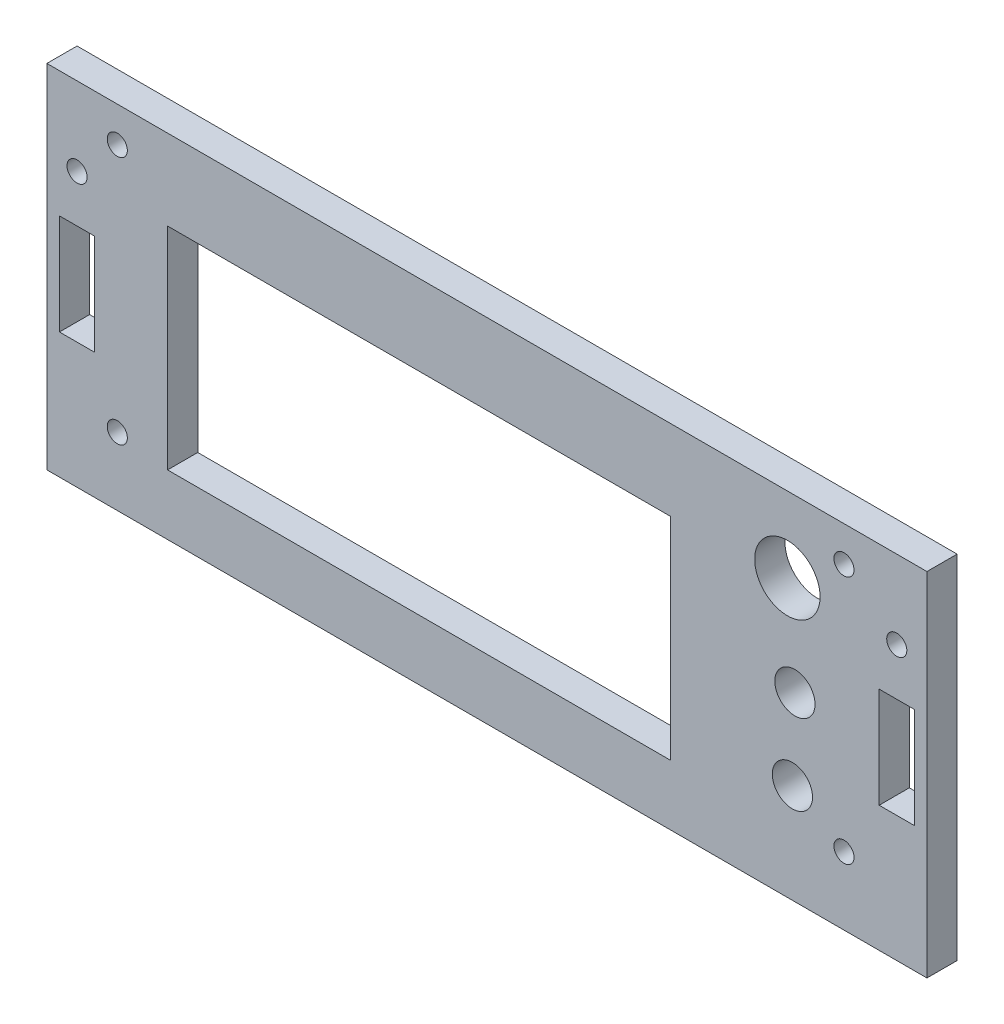
SolidWorks part; units mm, degrees
ref_plane "Plan de face" through (0, 0, 0) normal (0, 0, 1) x (1, 0, 0)
ref_plane "Plan de dessus" through (0, 0, 0) normal (0, 1, 0) x (1, 0, 0)
ref_plane "Plan de droite" through (0, 0, 0) normal (1, 0, 0) x (0, 0, -1)
sketch "Esquisse1" plane through (0, 0, 0) normal (0, 0, 1) x (1, 0, 0)
  line L1 (-87.5, 35) -> (87.5, 35)
  line L2 (-87.5, 35) -> (-87.5, -35)
  line L3 (-87.5, -35) -> (87.5, -35)
  line L4 (87.5, 35) -> (87.5, -35)
  line L5 (-87.5, 35) -> (87.5, -35) construction
  line L6 (-87.5, -35) -> (87.5, 35) construction
  line L7 (-63.5, 19) -> (36.5, 19)
  line L8 (-63.5, 19) -> (-63.5, -23)
  line L9 (-63.5, -23) -> (36.5, -23)
  line L10 (36.5, 19) -> (36.5, -23)
  line L11 (-63.5, 19) -> (36.5, -23) construction
  line L12 (-63.5, -23) -> (36.5, 19) construction
  point P0 (0, 0)
  point P6 (-13.5, -2)
  dimension "D1" = 175
  dimension "D2" = 70
  dimension "D3" = 100
  dimension "D4" = 42
  dimension "D5" = 24
  dimension "D6" = 12
extrude "Boss.-Extru.1" add sketch "Esquisse1" along normal blind 6
sketch "Esquisse2" plane through (0, 0, 6) normal (0, 0, 1) x (1, 0, 0)
  line L0 (-87.5, 0) -> (-81.5, 0) construction
  line L1 (-85, 10) -> (-78, 10)
  line L2 (-85, 10) -> (-85, -10)
  line L3 (-85, -10) -> (-78, -10)
  line L4 (-78, 10) -> (-78, -10)
  line L5 (-85, 10) -> (-78, -10) construction
  line L6 (-85, -10) -> (-78, 10) construction
  line L7 (-87.5, 35) -> (-87.5, -35) construction
  line L8 (-81.5, 0) -> (-81.5, 35) construction
  line L9 (87.5, 35) -> (-87.5, 35) construction
  circle A0 centre (-81.5, 19.4) radius 2
  point P0 (-81.5, 0)
  dimension "D4" = 4
  dimension "D1" = 7
  dimension "D2" = 20
  dimension "D3" = 6
  dimension "D5" = 15.6
extrude "Enlèv. mat.-Extru.1" cut sketch "Esquisse2" against normal blind 6
mirror "Symétrie1" about plane through (0, 0, 0) normal (1, 0, 0) of "Enlèv. mat.-Extru.1"
sketch "Esquisse3" plane through (0, 0, 6) normal (0, 0, 1) x (1, 0, 0)
  line L0 (-87.5, 35) -> (-87.5, -35) construction
  line L1 (-73.5, 28) -> (71, 28) construction
  line L2 (-73.5, 28) -> (-73.5, -21.5) construction
  line L3 (-73.5, -21.5) -> (71, -21.5) construction
  line L4 (71, 28) -> (71, -21.5) construction
  line L5 (-73.5, 28) -> (71, -21.5) construction
  line L6 (-73.5, -21.5) -> (71, 28) construction
  line L7 (87.5, 35) -> (-87.5, 35) construction
  circle A0 centre (-73.5, 28) radius 2
  circle A1 centre (71, 28) radius 2
  circle A2 centre (71, -21.5) radius 2
  circle A3 centre (-73.5, -21.5) radius 2
  circle A4 centre (59.75, 20) radius 6.5
  circle A5 centre (61.25, 1) radius 4
  circle A6 centre (60.75, -15.25) radius 4
  point P0 (-1.25, 3.25)
  dimension "D5" = 4
  dimension "D8" = 13
  dimension "D9" = 8
  dimension "D1" = 144.5
  dimension "D2" = 49.5
  dimension "D3" = 14
  dimension "D4" = 7
  dimension "D6" = 9.75
  dimension "D7" = 10.25
  dimension "D10" = 11.25
  dimension "D11" = 8
  dimension "D12" = 27
  dimension "D13" = 43.25
extrude "Enlèv. mat.-Extru.2" cut sketch "Esquisse3" against normal blind 6
